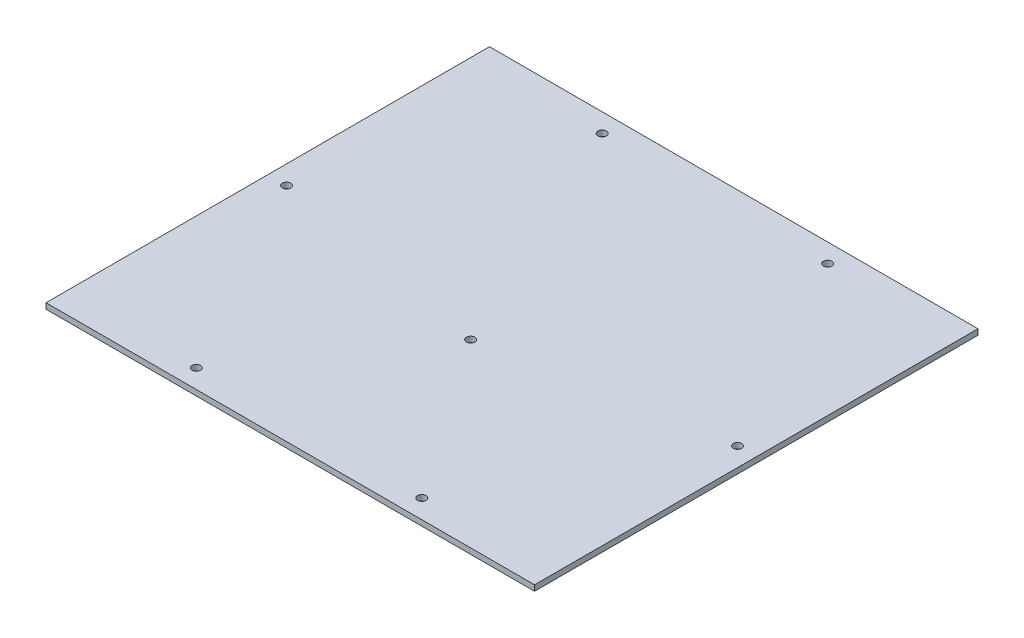
SolidWorks part; units mm, degrees
ref_plane "Спереди" through (0, 0, 0) normal (0, 0, 1) x (1, 0, 0)
ref_plane "Сверху" through (0, 0, 0) normal (0, 1, 0) x (1, 0, 0)
ref_plane "Справа" through (0, 0, 0) normal (1, 0, 0) x (0, 0, -1)
sketch "Эскиз1" plane through (0, 0, 0) normal (0, 1, 0) x (1, 0, 0)
  line L0 (0, 0) -> (260, 0)
  line L1 (0, 0) -> (0, 236)
  line L2 (260, 0) -> (260, 236)
  line L3 (0, 236) -> (260, 236)
  line L4 (10, 226) -> (250, 226) construction
  line L5 (10, 226) -> (10, 10) construction
  line L6 (250, 226) -> (250, 10) construction
  line L7 (10, 10) -> (250, 10) construction
  line L8 (70, 226) -> (70, 10) construction
  line L9 (190, 226) -> (190, 10) construction
  circle A0 centre (70, 226) radius 2.25
  circle A1 centre (190, 226) radius 2.25
  circle A2 centre (10, 118) radius 2.25
  circle A3 centre (250, 118) radius 2.25
  circle A4 centre (70, 10) radius 2.25
  circle A5 centre (190, 10) radius 2.25
  dimension "D7" = 70
  dimension "D8" = 70
  dimension "D9" = 4.5
  dimension "D10" = 4.5
  dimension "D11" = 4.5
  dimension "D12" = 4.5
  dimension "D13" = 4.5
  dimension "D14" = 4.5
  dimension "D1" = 236
  dimension "D2" = 260
  dimension "D3" = 10
  dimension "D4" = 10
  dimension "D5" = 10
  dimension "D6" = 10
extrude "Бобышка-Вытянуть1" add sketch "Эскиз1" along normal blind 3
sketch "Sketch1" plane through (0, 0, 0) normal (0, -1, 0) x (1, 0, 0)
  line L0 (240, -86) -> (20, -86) construction
  line L1 (240, -86) -> (20, -86) construction
  line L2 (130, -86) -> (130, -96) construction
  circle A0 centre (130, -96) radius 2.25
  dimension "D2" = 4.5
  dimension "D1" = 10
extrude "Cut-Extrude1" cut sketch "Sketch1" against normal through all
